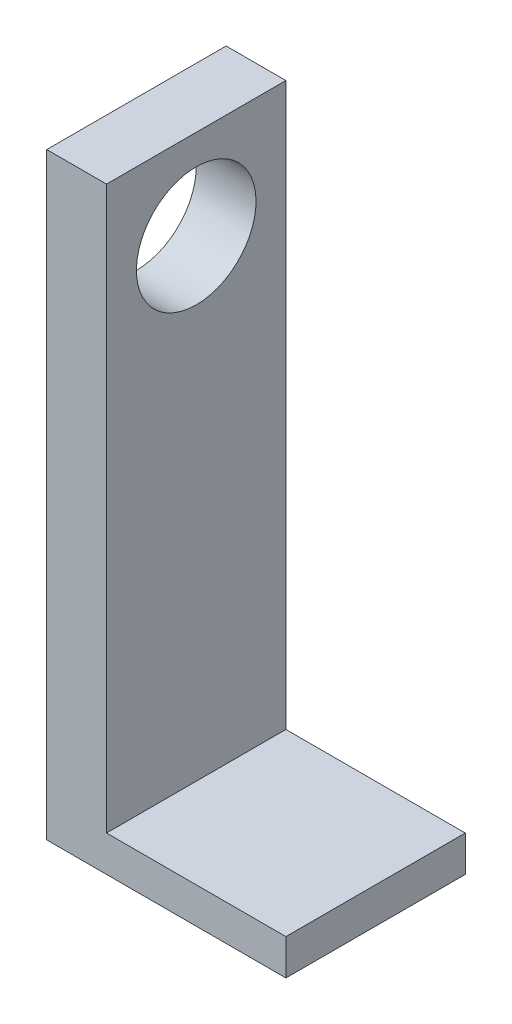
SolidWorks part; units mm, degrees
ref_plane "Plano frontal" through (0, 0, 0) normal (0, 0, 1) x (1, 0, 0)
ref_plane "Plano superior" through (0, 0, 0) normal (0, 1, 0) x (1, 0, 0)
ref_plane "Plano direito" through (0, 0, 0) normal (1, 0, 0) x (0, 0, -1)
sketch "Esboço1" plane through (0, 0, 0) normal (0, 0, 1) x (1, 0, 0)
  line L0 (0, 0) -> (20, 0)
  line L1 (20, 0) -> (20, 3)
  line L2 (20, 3) -> (5, 3)
  line L3 (5, 3) -> (5, 50)
  line L4 (5, 50) -> (0, 50)
  line L5 (0, 50) -> (0, 0)
  dimension "D1" = 20
  dimension "D2" = 3
  dimension "D3" = 50
  dimension "D4" = 5
extrude "Ressalto-extrusão1" add sketch "Esboço1" along normal blind 15
sketch "Esboço2" plane through (0, 0, 0) normal (-1, 0, 0) x (0, 0, 1)
  line L0 (7.5, 50) -> (7.5, 42.5) construction
  line L1 (15, 50) -> (0, 50) construction
  circle A0 centre (7.5, 42.5) radius 5
  dimension "D2" = 10
  dimension "D1" = 7.5
extrude "Corte-extrusão1" cut sketch "Esboço2" against normal through all
